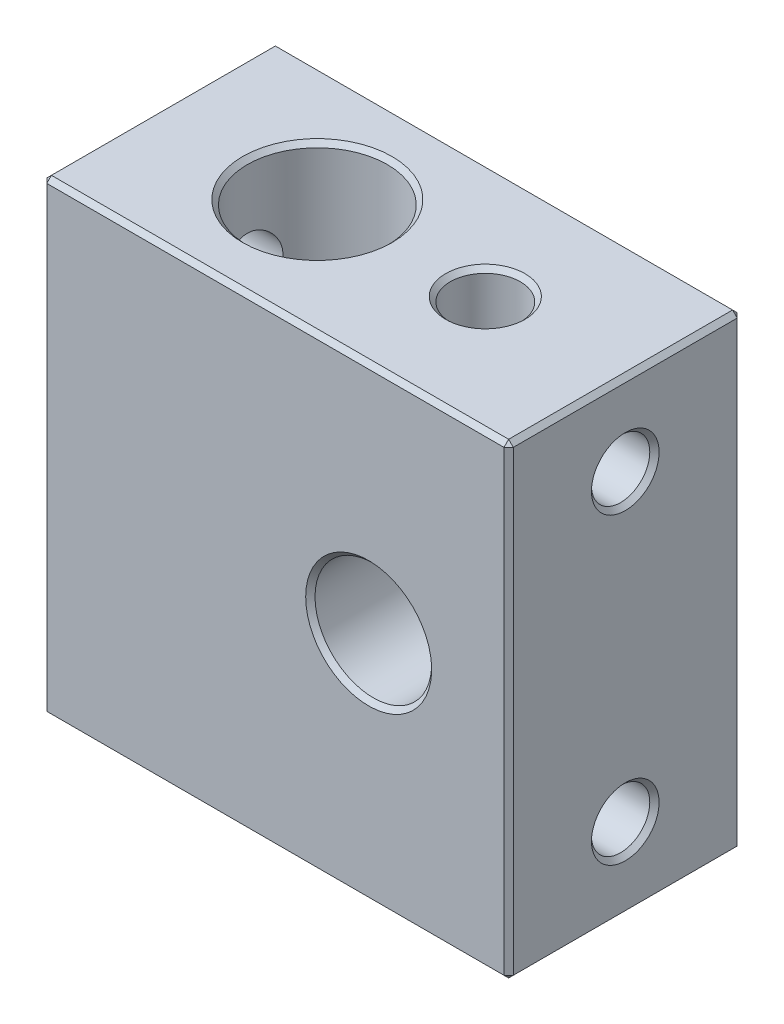
SolidWorks part; units mm, degrees
ref_plane "Спереди" through (0, 0, 0) normal (0, 0, 1) x (1, 0, 0)
ref_plane "Сверху" through (0, 0, 0) normal (0, 1, 0) x (1, 0, 0)
ref_plane "Справа" through (0, 0, 0) normal (1, 0, 0) x (0, 0, -1)
sketch "Эскиз1" plane through (0, 0, 0) normal (0, 0, 1) x (1, 0, 0)
  line L1 (0, 0) -> (20, 0)
  line L2 (0, 0) -> (0, 20)
  line L3 (0, 20) -> (20, 20)
  line L4 (20, 0) -> (20, 20)
  dimension "D1" = 20
  dimension "D2" = 20
extrude "Бобышка-Вытянуть1" add sketch "Эскиз1" along normal blind 10
sketch "Эскиз2" plane through (0, 0, 10) normal (0, 0, 1) x (1, 0, 0)
  line L0 (20, 0) -> (20, 20) construction
  circle A0 centre (14, 10) radius 2.5
  dimension "D1" = 6
extrude "Вырез-Вытянуть1" cut sketch "Эскиз2" against normal blind 10
sketch "Эскиз3" plane through (0, 0, 0) normal (0, -1, 0) x (1, 0, 0)
  line L0 (0, 10) -> (0, 0) construction
  line L1 (0, 10) -> (20, 10) construction
  circle A0 centre (6.8, 5) radius 3
  dimension "D1" = 6.8
  dimension "D2" = 5
extrude "Вырез-Вытянуть2" cut sketch "Эскиз3" against normal blind 20
sketch "Эскиз4" plane through (0, 0, 0) normal (-1, 0, 0) x (0, 0, 1)
  line L0 (10, 20) -> (0, 20) construction
  line L1 (10, 0) -> (0, 0) construction
  line L2 (0, 20) -> (0, 0) construction
  circle A0 centre (5, 16) radius 1.25
  circle A1 centre (5, 4) radius 1.25
  dimension "D1" = 4
  dimension "D2" = 4
  dimension "D3" = 5
  dimension "D4" = 5
extrude "Вырез-Вытянуть3" cut sketch "Эскиз4" against normal blind 6.7
sketch "Эскиз5" plane through (0, 0, 0) normal (0, -1, 0) x (1, 0, 0)
  line L0 (0, 10) -> (20, 10) construction
  line L1 (20, 10) -> (20, 0) construction
  circle A0 centre (14, 5) radius 1.5
  dimension "D1" = 5
  dimension "D2" = 6
extrude "Вырез-Вытянуть4" cut sketch "Эскиз5" against normal blind 6
sketch "Эскиз6" plane through (0, 20, 0) normal (0, 1, 0) x (1, 0, 0)
  line L0 (20, -10) -> (0, -10) construction
  line L1 (20, -10) -> (20, 0) construction
  circle A0 centre (14, -5) radius 1.5
  dimension "D1" = 5
  dimension "D2" = 6
extrude "Вырез-Вытянуть5" cut sketch "Эскиз6" against normal blind 6
sketch "Эскиз7" plane through (20, 0, 0) normal (1, 0, 0) x (0, 0, -1)
  line L0 (-10, 0) -> (0, 0) construction
  line L1 (-10, 20) -> (0, 20) construction
  line L2 (-10, 0) -> (-10, 20) construction
  circle A0 centre (-5, 3.5) radius 1.25
  circle A1 centre (-5, 16.5) radius 1.25
  dimension "D1" = 3.5
  dimension "D2" = 3.5
  dimension "D3" = 5
  dimension "D4" = 5
extrude "Вырез-Вытянуть6" cut sketch "Эскиз7" against normal blind 6
chamfer "Фаска1" distance 0.2 angle 45 22 edges at (6.8, 20, 2) (14, 20, 6.5) (6.8, 0, 2) (14, 0, 3.5) (0, 4, 6.25) (0, 16, 6.25) (16.5, 10, 0) (16.5, 10, 10) (20, 16.5, 3.75) (20, 3.5, 3.75) (20, 20, 5) (10, 20, 10) (0, 20, 5) (10, 20, 0) (0, 0, 5) (0, 10, 0) (10, 0, 0) (20, 10, 0) (20, 0, 5) (20, 10, 10) (10, 0, 10) (0, 10, 10)
